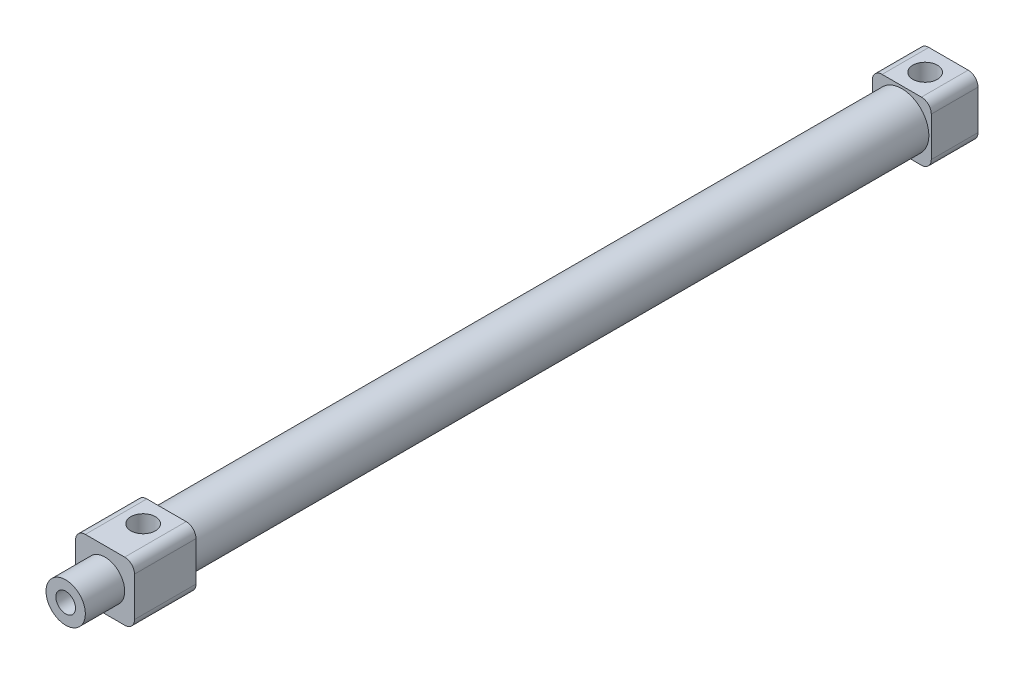
SolidWorks part; units mm, degrees
ref_plane "前视基准面" through (0, 0, 0) normal (0, 0, 1) x (1, 0, 0)
ref_plane "上视基准面" through (0, 0, 0) normal (0, 1, 0) x (1, 0, 0)
ref_plane "右视基准面" through (0, 0, 0) normal (1, 0, 0) x (0, 0, -1)
sketch "草图1" plane through (0, 0, 0) normal (0, 0, 1) x (1, 0, 0)
  line L1 (-6, -6) -> (6, -6)
  line L2 (-6, -6) -> (-6, 6)
  line L3 (-6, 6) -> (6, 6)
  line L4 (6, -6) -> (6, 6)
  line L5 (-6, -6) -> (6, 6) construction
  line L6 (-6, 6) -> (6, -6) construction
  point P0 (0, 0)
  dimension "D1" = 12
  dimension "D2" = 12
extrude "凸台-拉伸1" add sketch "草图1" along normal blind 9.5
sketch "草图2" plane through (0, 0, 9.5) normal (0, 0, 1) x (1, 0, 0)
  circle A0 centre (0, 0) radius 5.5
extrude "凸台-拉伸2" add sketch "草图2" along normal blind 149.5
sketch "草图3" plane through (0, 0, 159) normal (0, 0, 1) x (1, 0, 0)
  line L1 (-6, -6) -> (6, -6)
  line L2 (-6, -6) -> (-6, 6)
  line L3 (-6, 6) -> (6, 6)
  line L4 (6, -6) -> (6, 6)
  line L5 (-6, -6) -> (6, 6) construction
  line L6 (-6, 6) -> (6, -6) construction
  point P0 (0, 0)
extrude "凸台-拉伸3" add sketch "草图3" along normal blind 12.5
sketch "草图4" plane through (0, 0, 171.5) normal (0, 0, 1) x (1, 0, 0)
  circle A0 centre (0, 0) radius 4
extrude "凸台-拉伸4" add sketch "草图4" along normal blind 8
cosmetic thread "装饰螺纹线1" parameters "D2"=6.647
sketch "草图5" plane through (0, 0, 179.5) normal (0, 0, 1) x (1, 0, 0)
  circle A0 centre (0, 0) radius 2
extrude "切除-拉伸1" cut sketch "草图5" against normal offset from surface (178.5 mm away) 1 up to face at (0, 0, 0)
sketch "草图6" plane through (0, 6, 0) normal (0, 1, 0) x (1, 0, 0)
  line L0 (-6, -4.75) -> (6, -4.75) construction
  line L1 (-6, -9.5) -> (-6, 0) construction
  line L2 (6, -9.5) -> (6, 0) construction
  line L3 (-6, -163.75) -> (6, -163.75) construction
  line L5 (-6, -171.5) -> (-6, -159) construction
  line L6 (6, -171.5) -> (6, -159) construction
  line L7 (6, -159) -> (-6, -159) construction
  circle A0 centre (0, -4.75) radius 2.5
  circle A1 centre (0, -163.75) radius 2.5
  dimension "D1" = 5
  dimension "D2" = 4.75
extrude "切除-拉伸2" cut sketch "草图6" against normal up to surface (6 mm away)
cosmetic thread "装饰螺纹线2" parameters "D2"=6
cosmetic thread "装饰螺纹线3" parameters "D2"=6
fillet "圆角1" radius 2 8 edges at (6, 6, 4.75) (6, -6, 4.75) (-6, 6, 4.75) (-6, -6, 4.75) (-6, -6, 165.25) (6, -6, 165.25) (6, 6, 165.25) (-6, 6, 165.25)
